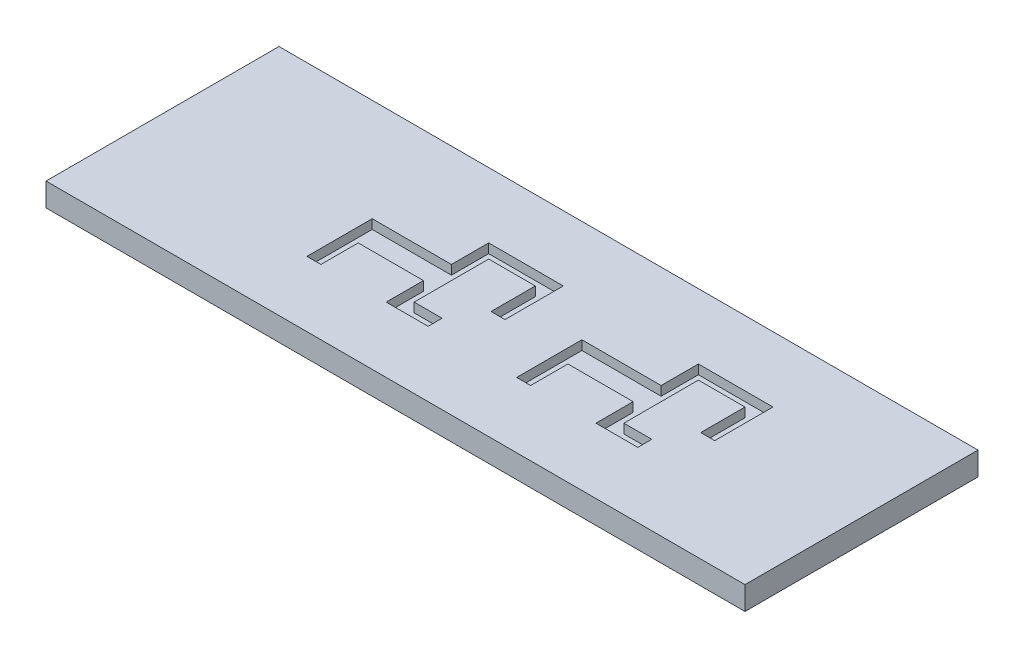
SolidWorks part; units mm, degrees
ref_plane "Front Plane" through (0, 0, 0) normal (0, 0, 1) x (1, 0, 0)
ref_plane "Top Plane" through (0, 0, 0) normal (0, 1, 0) x (1, 0, 0)
ref_plane "Right Plane" through (0, 0, 0) normal (1, 0, 0) x (0, 0, -1)
sketch "Sketch1" plane through (0, 0, 0) normal (0, 1, 0) x (1, 0, 0)
  line L1 (-37.5, -12.5) -> (37.5, -12.5)
  line L2 (-37.5, -12.5) -> (-37.5, 12.5)
  line L3 (-37.5, 12.5) -> (37.5, 12.5)
  line L4 (37.5, -12.5) -> (37.5, 12.5)
  line L5 (-37.5, -12.5) -> (37.5, 12.5) construction
  line L6 (-37.5, 12.5) -> (37.5, -12.5) construction
  point P0 (0, 0)
  dimension "D1" = 75
  dimension "D2" = 25
extrude "Boss-Extrude1" add sketch "Sketch1" along normal blind 2.5
sketch "Sketch2" plane through (0, 2.5, 0) normal (0, 1, 0) x (1, 0, 0)
  line L0 (-37.5, 0) -> (37.5, 0) construction
  line L1 (-37.5, 12.5) -> (-37.5, -12.5) construction
  line L2 (37.5, -12.5) -> (37.5, 12.5) construction
  line L3 (6, -1.5) -> (16, -1.5)
  line L4 (-16.5, -1.5) -> (-6.5, -1.5)
  line L5 (-16.5, -1.5) -> (-16.5, 1.5)
  line L6 (-16.5, 1.5) -> (-6.5, 1.5)
  line L7 (-6.5, -1.5) -> (-6.5, 1.5)
  line L8 (-16.5, -1.5) -> (-15, -1.5)
  line L9 (-16.5, -1.5) -> (-16.5, -5.5)
  line L10 (-16.5, -5.5) -> (-15, -5.5)
  line L11 (-15, -1.5) -> (-15, -5.5)
  line L12 (-37.5, 12.5) -> (-37.5, -12.5) construction
  line L13 (-6.5, 0) -> (-6.5, -1)
  line L16 (-6.5, -1.5) -> (-8, -1.5)
  line L17 (-6.5, -1.5) -> (-6.5, -4)
  line L18 (-6.5, -4) -> (-8, -4)
  line L19 (-8, -1.5) -> (-8, -4)
  line L20 (-6.5, 1.5) -> (-8, 1.5)
  line L21 (-6.5, 1.5) -> (-6.5, 4)
  line L22 (-6.5, 4) -> (-8, 4)
  line L23 (-8, 1.5) -> (-8, 4)
  line L24 (-8, 4) -> (0, 4)
  line L25 (-8, 4) -> (-8, 5.5)
  line L26 (-8, 5.5) -> (0, 5.5)
  line L27 (0, 4) -> (0, 5.5)
  line L28 (-8, -4) -> (-3.5, -4)
  line L29 (-8, -4) -> (-8, -5.5)
  line L30 (-8, -5.5) -> (-3.5, -5.5)
  line L31 (-3.5, -4) -> (-3.5, -5.5)
  line L32 (6, -1.5) -> (6, 1.5)
  line L33 (6, 1.5) -> (16, 1.5)
  line L34 (16, -1.5) -> (16, 1.5)
  line L35 (6, -1.5) -> (7.5, -1.5)
  line L36 (6, -1.5) -> (6, -5.5)
  line L37 (6, -5.5) -> (7.5, -5.5)
  line L38 (7.5, -1.5) -> (7.5, -5.5)
  line L40 (16, 0) -> (16, -1)
  line L43 (16, -1.5) -> (14.5, -1.5)
  line L44 (16, -1.5) -> (16, -4)
  line L45 (16, -4) -> (14.5, -4)
  line L46 (14.5, -1.5) -> (14.5, -4)
  line L47 (16, 1.5) -> (14.5, 1.5)
  line L48 (16, 1.5) -> (16, 4)
  line L49 (16, 4) -> (14.5, 4)
  line L50 (14.5, 1.5) -> (14.5, 4)
  line L51 (14.5, 4) -> (22.5, 4)
  line L52 (14.5, 4) -> (14.5, 5.5)
  line L53 (14.5, 5.5) -> (22.5, 5.5)
  line L54 (22.5, 4) -> (22.5, 5.5)
  line L55 (14.5, -4) -> (19, -4)
  line L56 (14.5, -4) -> (14.5, -5.5)
  line L57 (14.5, -5.5) -> (19, -5.5)
  line L58 (19, -4) -> (19, -5.5)
  line L60 (0, 4) -> (-1.5, 4)
  line L61 (0, 4) -> (0, -0.75)
  line L62 (0, -0.75) -> (-1.5, -0.75)
  line L63 (-1.5, 4) -> (-1.5, -0.75)
  line L64 (22.5, 4) -> (21, 4)
  line L65 (22.5, 4) -> (22.5, -0.75)
  line L66 (22.5, -0.75) -> (21, -0.75)
  line L67 (21, 4) -> (21, -0.75)
  point P6 (-16.5025, 0)
  point P30 (-16.5, 0)
  point P54 (6, 0)
  dimension "D1" = 3
  dimension "D2" = 1.5
  dimension "D3" = 1.5
  dimension "D4" = 1.5
  dimension "D5" = 21
  dimension "D6" = 12.5
  dimension "D7" = 1.5
  dimension "D8" = 1.5
  dimension "D9" = 4
  dimension "D10" = 2.5
  dimension "D11" = 2.5
  dimension "D13" = 8
  dimension "D14" = 4.5
  dimension "D15" = 10
  dimension "D16" = 3
  dimension "D17" = 1.5
  dimension "D18" = 1.5
  dimension "D19" = 1.5
  dimension "D22" = 1.5
  dimension "D23" = 1.5
  dimension "D24" = 4
  dimension "D25" = 2.5
  dimension "D26" = 2.5
  dimension "D28" = 8
  dimension "D29" = 4.5
  dimension "D30" = 10
  dimension "D31" = 1.5
  dimension "D32" = 4.75
  dimension "D33" = 1.5
  dimension "D34" = 4.75
extrude "Cut-Extrude1" cut sketch "Sketch2" against normal blind 1 contours L5 L0 L13 L7 L6 | L0 L5 L4 L7 | L11 L4 L9 L10 | L31 L28 L18 L29 L30 | L4 L19 L18 L17 | L23 L6 L21 L22 | L24 L27 L26 L25 L22 | L63 L0 L61 L24 | L0 L32 L3 L34 | L32 L0 L40 L34 L33 | L38 L3 L36 L37 | L3 L46 L45 L44 | L58 L55 L45 L56 L57 | L50 L33 L48 L49 | L51 L54 L53 L52 L49 | L67 L0 L65 L51 | L0 L67 L66 L65
